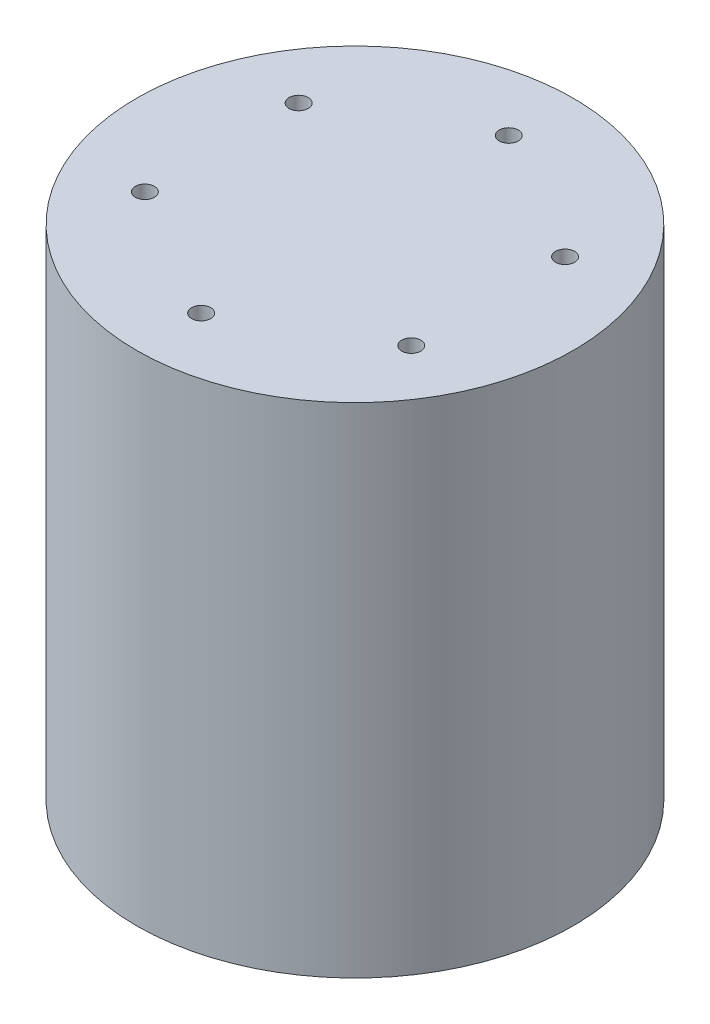
SolidWorks part; units mm, degrees
ref_plane "Alzado" through (0, 0, 0) normal (0, 0, 1) x (1, 0, 0)
ref_plane "Planta" through (0, 0, 0) normal (0, 1, 0) x (1, 0, 0)
ref_plane "Vista lateral" through (0, 0, 0) normal (1, 0, 0) x (0, 0, -1)
sketch "Croquis1" plane through (0, 0, 0) normal (0, 1, 0) x (1, 0, 0)
  circle A0 centre (0, 0) radius 35.5
  dimension "D1" = 71
extrude "Saliente-Extruir1" add sketch "Croquis1" along normal blind 81
sketch "Croquis2" plane through (0, 0, 0) normal (0, -1, 0) x (1, 0, 0)
  circle A0 centre (0, 0) radius 20
  circle A1 centre (0, 0) radius 26
  dimension "D1" = 40
  dimension "D2" = 52
extrude "Cortar-Extruir1" cut sketch "Croquis2" against normal blind 7
sketch "Croquis3" plane through (0, 0, 0) normal (0, -1, 0) x (1, 0, 0)
  circle A0 centre (0, 0) radius 15 construction
  circle A1 centre (0, 15) radius 1.6
  circle A2 centre (14.2658, 4.6353) radius 1.6
  circle A3 centre (8.8168, -12.1353) radius 1.6
  circle A4 centre (-8.8168, -12.1353) radius 1.6
  circle A5 centre (-14.2658, 4.6353) radius 1.6
  point P16 (0, 0)
  dimension "D1" = 3.2
  dimension "D2" = 30
  dimension "D3" = 5
extrude "Cortar-Extruir2" cut sketch "Croquis3" against normal blind 7
sketch "Croquis4" plane through (0, 81, 0) normal (0, 1, 0) x (1, 0, 0)
  circle A0 centre (0, 0) radius 25 construction
  circle A1 centre (0, 25) radius 1.55
  circle A2 centre (21.6506, 12.5) radius 1.55
  circle A3 centre (21.6506, -12.5) radius 1.55
  circle A4 centre (0, -25) radius 1.55
  circle A5 centre (-21.6506, -12.5) radius 1.55
  circle A6 centre (-21.6506, 12.5) radius 1.55
  point P18 (0, 0)
  dimension "D1" = 3.1
  dimension "D3" = 50
  dimension "D2" = 6
extrude "Cortar-Extruir3" cut sketch "Croquis4" against normal blind 7
